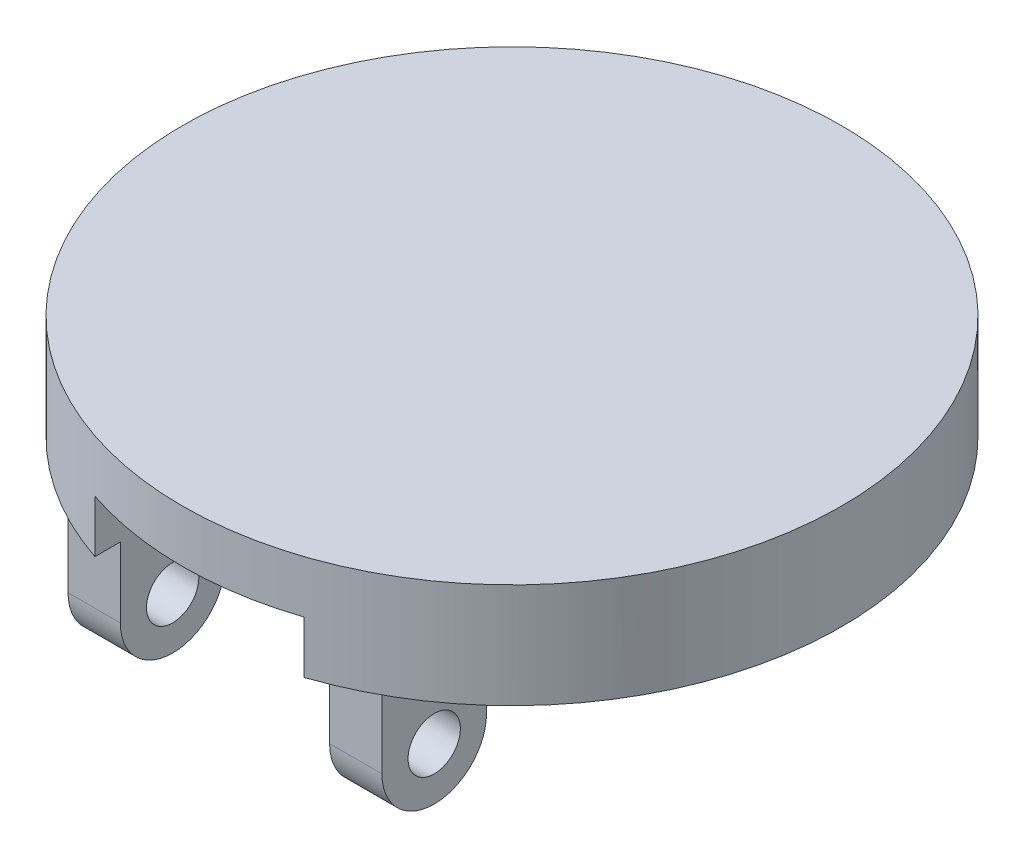
SolidWorks part; units mm, degrees
ref_plane "Front Plane" through (0, 0, 0) normal (0, 0, 1) x (1, 0, 0)
ref_plane "Top Plane" through (0, 0, 0) normal (0, 1, 0) x (1, 0, 0)
ref_plane "Right Plane" through (0, 0, 0) normal (1, 0, 0) x (0, 0, -1)
ref_plane "Plane1" through (6.35, 0, 0) normal (1, 0, 0) x (0, 0, -1)
sketch "Sketch1" plane through (0, 0, 0) normal (0, 1, 0) x (1, 0, 0)
  circle A0 centre (0, 0) radius 20
  point P3 (0, 0)
  dimension "D1" = 40
extrude "Boss-Extrude1" add sketch "Sketch1" along normal blind 6.35
sketch "Sketch2" plane through (6.35, 0, 0) normal (1, 0, 0) x (0, 0, -1)
  line L0 (-17.4201, 0) -> (-17.4201, -4.254)
  line L1 (-5.8492, 6.35) -> (-11.0701, 6.35)
  line L2 (-5.8492, 6.35) -> (-5.8492, 0)
  line L3 (-5.8492, 0) -> (-7.8951, 0)
  line L8 (-11.0701, -3.175) -> (-11.0701, -4.254)
  line L9 (-9.525, -0.254) -> (-18.9652, -0.254) construction
  line L10 (-18.9652, -8.254) -> (-18.9652, -0.254) construction
  arc A0 (-17.4201, -4.254) -> (-11.0701, -4.254) centre (-14.2451, -4.254) ccw
  arc A1 (-11.0701, 6.35) -> (-17.4201, 0) centre (-11.0701, 0) ccw
  arc A2 (-7.8951, 0) -> (-11.0701, -3.175) centre (-7.8951, -3.175) ccw
  point P7 (-14.2451, -0.254)
  point P10 (-18.9652, -4.254)
  point P11 (0, 0)
  point P14 (0, 0)
  dimension "D2" = 6.35
  dimension "D3" = 3.175
  dimension "D1" = 6.35
  dimension "D4" = 6.35
  dimension "D5" = 0.254
extrude "Boss-Extrude2" add sketch "Sketch2" along normal blind 3.175
mirror "Mirror1" about plane through (0, 0, 0) normal (1, 0, 0) of "Boss-Extrude2"
sketch "Sketch3" plane through (9.525, 0, 0) normal (1, 0, 0) x (0, 0, -1)
  circle A0 centre (-14.2451, -4.254) radius 1.5875
  arc A1 (-17.4201, -4.254) -> (-11.0701, -4.254) centre (-14.2451, -4.254) ccw construction
  dimension "D1" = 3.175
extrude "Cut-Extrude1" cut sketch "Sketch3" against normal through all
sketch "Sketch5" plane through (0, 0, 0) normal (0, -1, 0) x (1, 0, 0)
  line L0 (6.35, 17.4201) -> (6.35, 7.8951) construction
  line L1 (-6.35, 7.8951) -> (-6.35, 17.4201) construction
  line L2 (6.35, 18.9652) -> (6.35, 7.6056)
  line L3 (-6.35, 7.6056) -> (-6.35, 18.9652)
  arc A0 (-6.35, 7.6056) -> (6.35, 7.6056) centre (0, 0) ccw
  circle A1 centre (0, 0) radius 20 construction
  arc A2 (6.35, 18.9652) -> (-6.35, 18.9652) centre (0, 0) ccw
extrude "Cut-Extrude2" cut sketch "Sketch5" against normal blind 3.175
